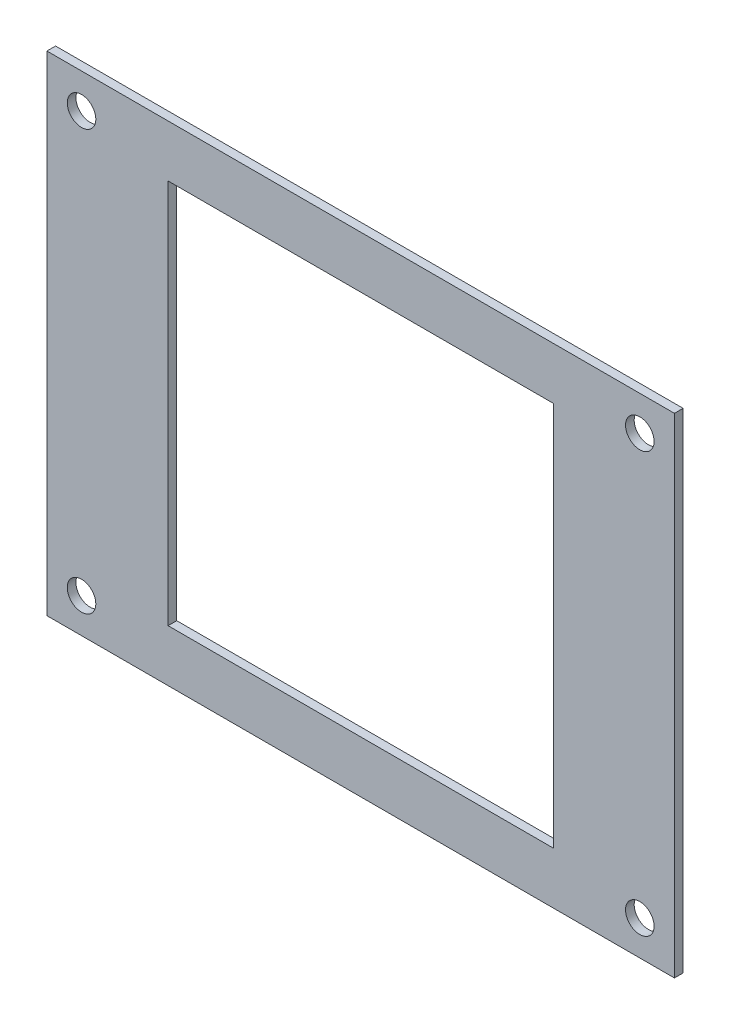
SolidWorks part; units mm, degrees
ref_plane "Front Plane" through (0, 0, 0) normal (1, 0, 0) x (0, 1, 0)
ref_plane "Top Plane" through (0, 0, 0) normal (0, 0, 1) x (0, 1, 0)
ref_plane "Right Plane" through (0, 0, 0) normal (0, 1, 0) x (-1, 0, 0)
sketch "Sketch1" plane through (0, 0, 0) normal (0, 0, 1) x (0, 1, 0)
  line L1 (0, 0) -> (56.5, 0)
  line L2 (0, 0) -> (0, 72.5)
  line L3 (0, 72.5) -> (56.5, 72.5)
  line L4 (56.5, 0) -> (56.5, 72.5)
  line L5 (6, 14) -> (50.5, 14)
  line L6 (6, 14) -> (6, 58.5)
  line L7 (6, 58.5) -> (50.5, 58.5)
  line L8 (50.5, 14) -> (50.5, 58.5)
  circle A0 centre (4, 68.5) radius 1.65
  circle A1 centre (52.5, 68.5) radius 1.65
  circle A2 centre (52.5, 4) radius 1.65
  circle A3 centre (4, 4) radius 1.65
  dimension "D3" = 3.3
  dimension "D4" = 4
  dimension "D5" = 4
  dimension "D6" = 4
  dimension "D7" = 4
  dimension "D8" = 4
  dimension "D9" = 4
  dimension "D10" = 4
  dimension "D11" = 4
  dimension "D1" = 72.5
  dimension "D2" = 56.5
  dimension "D12" = 44.5
  dimension "D13" = 44.5
  dimension "D14" = 6
  dimension "D15" = 14
extrude "Boss-Extrude1" add sketch "Sketch1" along normal blind 1
